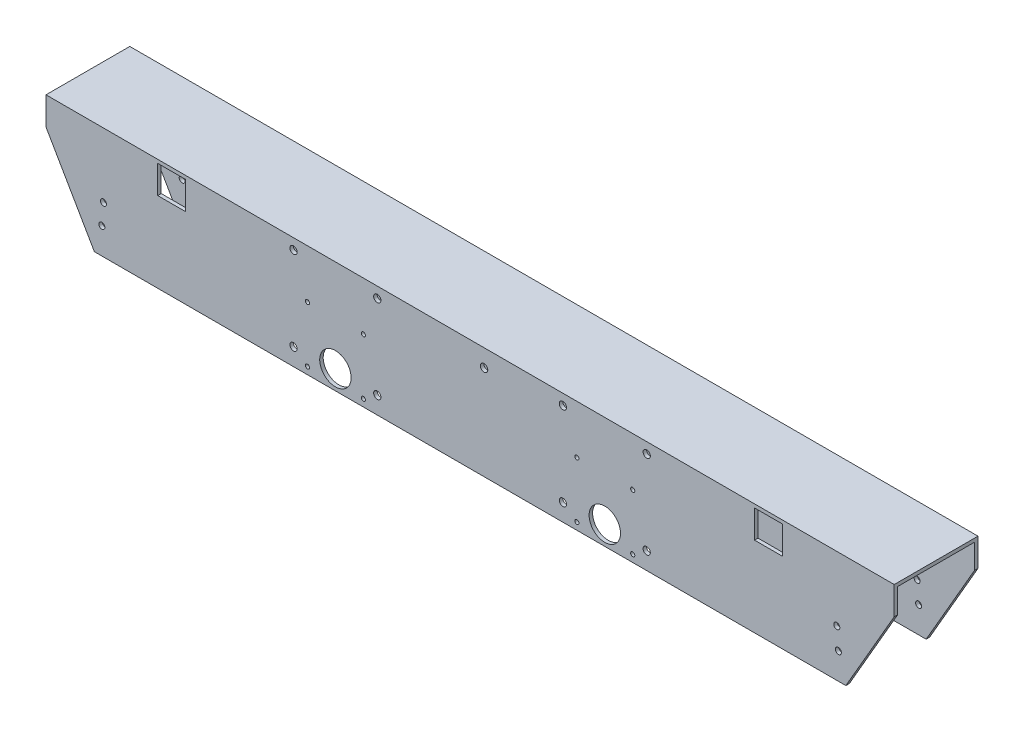
SolidWorks part; units mm, degrees
ref_plane "Front Plane" through (0, 0, 0) normal (0, 0, 1) x (1, 0, 0)
ref_plane "Top Plane" through (0, 0, 0) normal (0, 1, 0) x (1, 0, 0)
ref_plane "Right Plane" through (0, 0, 0) normal (1, 0, 0) x (0, 0, -1)
sketch "Sketch1" plane through (0, 0, 0) normal (1, 0, 0) x (0, 0, -1)
  line L0 (-34.925, 47.625) -> (-34.925, -47.625) construction
  line L1 (-38.1, 50.8) -> (38.1, 50.8)
  line L2 (-38.1, 50.8) -> (-38.1, -50.8)
  line L3 (-38.1, -50.8) -> (-34.925, -50.8)
  line L4 (38.1, 50.8) -> (38.1, -50.8)
  line L5 (-38.1, 50.8) -> (38.1, -50.8) construction
  line L6 (-38.1, -50.8) -> (38.1, 50.8) construction
  line L7 (34.925, 47.625) -> (34.925, -50.8)
  line L8 (-34.925, 47.625) -> (34.925, 47.625)
  line L9 (-34.925, 47.625) -> (-34.925, -50.8)
  line L10 (-34.925, -47.625) -> (34.925, -47.625) construction
  line L11 (34.925, 47.625) -> (34.925, -47.625) construction
  line L12 (-38.1, -50.8) -> (38.1, -50.8) construction
  line L13 (38.1, -50.8) -> (34.925, -50.8)
  point P0 (0, 0)
  dimension "D1" = 76.2
  dimension "D2" = 101.6
  dimension "D3" = 3.175
extrude "Boss-Extrude1" add sketch "Sketch1" along normal mid plane 771.4115
sketch "Sketch2" plane through (0, 0, 38.1) normal (0, 0, 1) x (1, 0, 0)
  line L1 (-385.7058, 50.8) -> (-385.7058, -50.8) construction
  line L8 (385.7058, -50.8) -> (-385.7058, -50.8) construction
  line L9 (0, -41.91) -> (0, 41.91) construction
  line L13 (0, 50.8) -> (0, -55.872) construction
  line L14 (385.7058, 50.8) -> (-385.7058, 50.8) construction
  circle A0 centre (-333.4758, -7.9375) radius 2.75
  circle A1 centre (122.5004, -33.3375) radius 14.2875
  circle A2 centre (333.4758, -7.9375) radius 2.75
  circle A3 centre (334.9026, -26.9276) radius 2.75
  circle A6 centre (-122.5004, -33.3375) radius 14.2875
  circle A7 centre (-334.9026, -26.9276) radius 2.75
  dimension "D1" = 122.5004
  dimension "D2" = 17.4625
  dimension "D3" = 212.4989
  dimension "D4" = 210.9754
  dimension "D5" = 28.575
  dimension "D6" = 25.4
  dimension "D7" = 5.5
  dimension "D8" = 52.2299
  dimension "D9" = 28.575
  dimension "D10" = 5.5
  dimension "D11" = 212.4989
  dimension "D12" = 25.4
  dimension "D13" = 17.4625
  dimension "D15" = 5.5
  dimension "D16" = 18.9901
  dimension "D14" = 19.0436
extrude "Cut-Extrude1" cut sketch "Sketch2" against normal blind 141.732
sketch "Sketch14" plane through (0, 0, -38.1) normal (0, 0, -1) x (-1, 0, 0)
  line L0 (-385.7058, -50.8) -> (385.7058, -50.8) construction
  line L1 (0, 54.2422) -> (0, -54.1107) construction
  line L2 (0, 41.91) -> (0, -41.91) construction
  circle A0 centre (-160.6004, -35.1235) radius 3.302
  circle A1 centre (-160.6118, 41.0765) radius 3.302
  circle A2 centre (-84.4118, 41.0765) radius 3.302
  circle A3 centre (-84.4118, -35.1235) radius 3.302
  circle A4 centre (-122.5004, -33.3375) radius 14.2875 construction
  circle A6 centre (160.6004, -35.1235) radius 3.302
  circle A7 centre (84.4118, -35.1235) radius 3.302
  circle A8 centre (84.4118, 41.0765) radius 3.302
  circle A9 centre (160.6118, 41.0765) radius 3.302
  dimension "D1" = 6.604
  dimension "D2" = 15.6765
  dimension "D3" = 76.2
  dimension "D4" = 76.2
  dimension "D5" = 76.2
  dimension "D6" = 38.1
extrude "Cut-Extrude12" cut sketch "Sketch14" against normal through all
sketch "Sketch16" plane through (0, 0, 38.1) normal (0, 0, 1) x (1, 0, 0)
  line L1 (-385.7058, 50.8) -> (-385.7058, -50.8) construction
  line L2 (-385.7058, 25.4) -> (-341.7117, -50.8)
  line L3 (385.7058, -50.8) -> (-385.7058, -50.8) construction
  line L4 (-341.7117, -50.8) -> (-385.7058, -50.8)
  line L5 (-385.7058, -50.8) -> (-385.7058, 25.4)
  line L6 (0, 50.8) -> (0, -65.171) construction
  line L7 (0, -41.91) -> (0, 41.91) construction
  line L9 (341.7117, -50.8) -> (385.7058, -50.8)
  line L10 (385.7058, -50.8) -> (385.7058, 25.4)
  line L11 (385.7058, 25.4) -> (341.7117, -50.8)
  dimension "D1" = 60
  dimension "D2" = 76.2
  dimension "D4" = 43.9941
extrude "Cut-Extrude13" cut sketch "Sketch16" against normal blind 101.6
sketch "Sketch17" plane through (0, 0, -38.1) normal (0, 0, -1) x (-1, 0, 0)
  line L0 (0, 41.91) -> (0, -41.91) construction
  line L1 (-25.4, 47.625) -> (0, 47.625)
  line L2 (-25.4, 47.625) -> (-25.4, 22.225)
  line L3 (-25.4, 22.225) -> (0, 22.225)
  line L4 (0, 47.625) -> (0, 22.225)
  line L7 (260.54, 47.625) -> (285.94, 47.625)
  line L8 (260.54, 47.625) -> (260.54, 22.225)
  line L9 (260.54, 22.225) -> (285.94, 22.225)
  line L10 (285.94, 47.625) -> (285.94, 22.225)
  dimension "D1" = 25.4
  dimension "D2" = 25.4
  dimension "D3" = 25.4
  dimension "D4" = 25.4
extrude "Cut-Extrude19" cut sketch "Sketch17" against normal blind 25.4
hole_wizard "1/4 Clearance Hole1" positions "Sketch21" profile "Sketch20" hole size "1/4" standard "ANSI Inch" end condition through all
sketch "Sketch21" plane through (0, 0, -38.1) normal (0, 0, -1) x (-1, 0, 0)
  line L0 (-385.7058, 47.625) -> (385.7058, 47.625) construction
  line L1 (285.94, 22.225) -> (285.94, 47.625) construction
  line L2 (-25.4, 22.225) -> (0, 22.225) construction
  line L3 (-25.4, 47.625) -> (-25.4, 22.225) construction
  point P0 (-12.7, 34.925)
  point P2 (273.24, 34.925)
  dimension "D1" = 12.7
  dimension "D2" = 12.7
  dimension "D3" = 12.7
  dimension "D4" = 12.7
sketch "Sketch20" plane through (12.7, 34.925, -38.1) normal (1, 0, 0) x (0, 1, 0)
  line L0 (0, 0) -> (0, 76.2)
  line L1 (0, 76.2) -> (3.3782, 76.2)
  line L2 (3.3782, 76.2) -> (3.3782, 0)
  line L5 (3.3782, 0) -> (0, 0)
  line L11 (0, -6.35) -> (0, 107.95) construction
  dimension "Thru Hole Dia." = 6.7564
  dimension "Thru Hole Depth" = 76.2
hole_wizard "#6 Clearance Hole1" positions "Sketch23" profile "Sketch22" hole size "#6" standard "ANSI Inch" end condition through all
sketch "Sketch23" plane through (0, 0, 38.1) normal (0, 0, 1) x (1, 0, 0)
  line L0 (0, 50.8) -> (0, -50.2315) construction
  line L1 (385.7058, 50.8) -> (-385.7058, 50.8) construction
  line L2 (0, -41.91) -> (0, 41.91) construction
  line L3 (341.7117, -50.8) -> (-341.7117, -50.8) construction
  circle A0 centre (-122.5004, -33.3375) radius 14.2875 construction
  point P0 (-147.9004, -44.3)
  point P2 (-97.1004, -44.3)
  point P18 (97.1004, -44.3)
  point P20 (147.9004, -44.3)
  point P28 (-147.9004, 6.5)
  point P30 (-97.1004, 6.5)
  point P38 (97.1004, 6.5)
  point P39 (147.9004, 6.5)
  dimension "D2" = 25.4
  dimension "D1" = 50.8
  dimension "D3" = 6.5
  dimension "D4" = 50.8
  dimension "D5" = 50.8
  dimension "D6" = 50.8
sketch "Sketch22" plane through (-147.9004, -44.3, 38.1) normal (1, 0, 0) x (0, -1, 0)
  line L0 (0, 0) -> (0, 76.2)
  line L1 (0, 76.2) -> (1.8986, 76.2)
  line L2 (1.8986, 76.2) -> (1.8986, 0)
  line L5 (1.8986, 0) -> (0, 0)
  line L11 (0, -6.35) -> (0, 107.95) construction
  dimension "Thru Hole Dia." = 3.7973
  dimension "Thru Hole Depth" = 76.2
sketch "Sketch25" plane through (0, 0, 38.1) normal (0, 0, 1) x (1, 0, 0)
  line L0 (385.7058, 50.8) -> (-385.7058, 50.8) construction
  line L1 (0, 50.8) -> (0, -49.4773) construction
  line L2 (0, -41.91) -> (0, 41.91) construction
  line L3 (284.1058, 22.225) -> (258.7058, 22.225)
  line L4 (284.1058, 47.625) -> (284.1058, 22.225)
  line L5 (-385.7058, 50.8) -> (-385.7058, 25.4) construction
  line L6 (-284.1058, 47.625) -> (-258.7058, 47.625)
  line L7 (-284.1058, 47.625) -> (-284.1058, 22.225)
  line L8 (-284.1058, 22.225) -> (-258.7058, 22.225)
  line L9 (-258.7058, 47.625) -> (-258.7058, 22.225)
  line L10 (258.7058, 47.625) -> (258.7058, 22.225)
  line L11 (284.1058, 47.625) -> (258.7058, 47.625)
  line L12 (385.7058, 50.8) -> (385.7058, 25.4) construction
  dimension "D1" = 101.6
  dimension "D6" = 101.6
  dimension "D7" = 25.4
  dimension "D8" = 25.4
  dimension "D9" = 3.175
extrude "Cut-Extrude20" cut sketch "Sketch25" against normal up to next
hole_wizard "#6 Clearance Hole2" positions "Sketch29" profile "Sketch28" hole size "#6" standard "ANSI Inch" end condition through all
sketch "Sketch29" plane through (0, 0, -34.925) normal (0, 0, 1) x (1, 0, 0)
  line L0 (-258.7058, 22.225) -> (-258.7058, 47.625) construction
  line L1 (-284.1058, 22.225) -> (-258.7058, 22.225) construction
  line L2 (0, 50.8) -> (0, -56.4556) construction
  line L3 (385.7058, 50.8) -> (-385.7058, 50.8) construction
  line L4 (0, -41.91) -> (0, 41.91) construction
  point P0 (-271.4058, 34.925)
  point P16 (271.4058, 34.925)
  dimension "D1" = 12.7
  dimension "D2" = 12.7
sketch "Sketch28" plane through (-271.4058, 34.925, -34.925) normal (1, 0, 0) x (0, -1, 0)
  line L0 (0, 0) -> (0, 3.175)
  line L1 (0, 3.175) -> (1.8986, 3.175)
  line L2 (1.8986, 3.175) -> (1.8986, 0)
  line L5 (1.8986, 0) -> (0, 0)
  line L11 (0, -6.35) -> (0, 107.95) construction
  dimension "Thru Hole Dia." = 3.7973
  dimension "Thru Hole Depth" = 3.175
